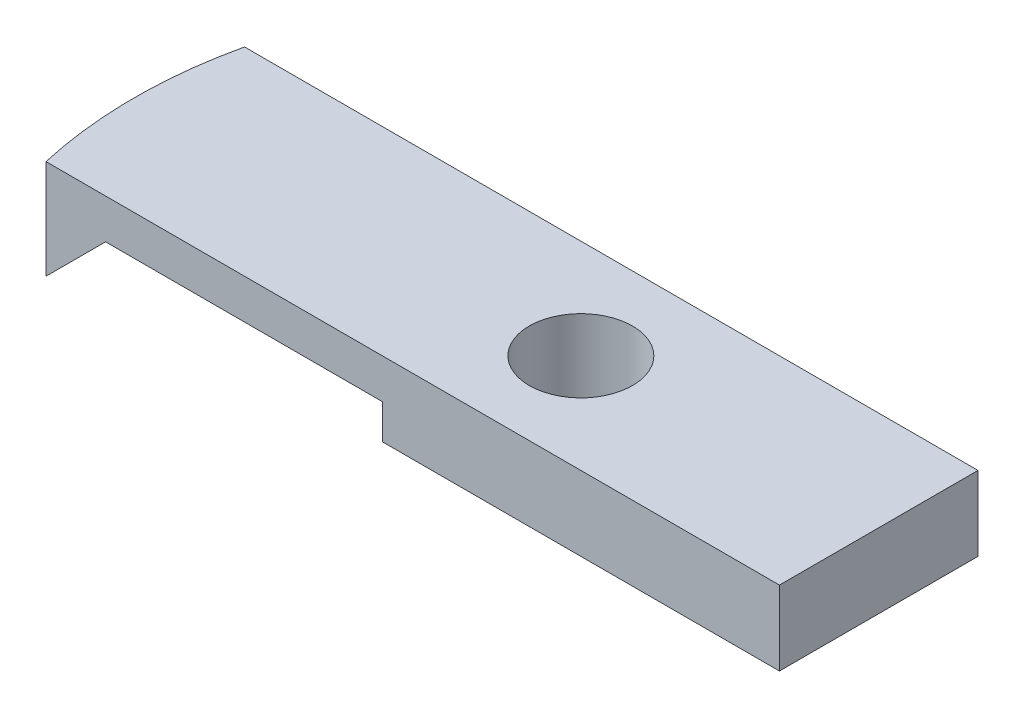
SolidWorks part; units mm, degrees
ref_plane "Front Plane" through (0, 0, 0) normal (0, 0, 1) x (1, 0, 0)
ref_plane "Top Plane" through (0, 0, 0) normal (0, 1, 0) x (1, 0, 0)
ref_plane "Right Plane" through (0, 0, 0) normal (1, 0, 0) x (0, 0, -1)
sketch "Sketch1" plane through (0, 0, 0) normal (0, 1, 0) x (1, 0, 0)
  line L0 (0, 0) -> (-28.575, 0) construction
  line L1 (19.05, 6.35) -> (19.05, -6.35)
  line L2 (0, 0) -> (19.05, 0) construction
  line L3 (19.05, 6.35) -> (-27.8605, 6.35)
  line L4 (-27.8605, 6.35) -> (-27.8605, -6.35) construction
  line L5 (-27.8605, -6.35) -> (19.05, -6.35)
  circle A0 centre (0, 0) radius 3.302
  circle A1 centre (0, 0) radius 28.575 construction
  arc A2 (-27.8605, 6.35) -> (-27.8605, -6.35) centre (0, 0) ccw
  dimension "D2" = 6.604
  dimension "D1" = 28.575
  dimension "D3" = 12.7
  dimension "D4" = 19.05
extrude "Boss-Extrude1" add sketch "Sketch1" along normal blind 6.35
sketch "Sketch2" plane through (0, 0, 6.35) normal (0, 0, 1) x (1, 0, 0)
  line L0 (19.05, 1.5875) -> (-27.8605, 1.5875)
  line L1 (19.05, 6.35) -> (19.05, 0) construction
  line L2 (-27.8605, 6.35) -> (-27.8605, 0) construction
  line L3 (-27.8605, 0) -> (-26.273, 1.5875)
  line L4 (-26.273, 1.5875) -> (-26.273, 3.81) construction
  line L5 (-26.273, 3.81) -> (-6.35, 3.81)
  line L6 (-6.35, 3.81) -> (-6.35, 1.5875)
  line L7 (-27.8605, 0) -> (19.05, 0)
  line L8 (19.05, 0) -> (19.05, 6.35)
  line L9 (19.05, 6.35) -> (-27.8605, 6.35)
  line L10 (-27.8605, 6.35) -> (-27.8605, 0)
  line L11 (-27.8605, 0) -> (19.05, 0)
  line L12 (19.05, 0) -> (19.05, 6.35)
  line L13 (19.05, 6.35) -> (-27.8605, 6.35)
  line L14 (-27.8605, 6.35) -> (-27.8605, 0)
  line L15 (-26.273, 1.5875) -> (-24.0505, 3.81)
  line L16 (0, 0) -> (0, 6.35) construction
  line M12 (-27.8605, 0) -> (19.05, 0)
  line M13 (19.05, 0) -> (19.05, 6.35)
  dimension "D2" = 1.5875
  dimension "D3" = 45
  dimension "D4" = 2.54
  dimension "D5" = 6.35
  dimension "D1" = 0
extrude "Cut-Extrude1" cut sketch "Sketch2" against normal through all contours L3 L0 M12 M13 | L15 L0 L6 L5
